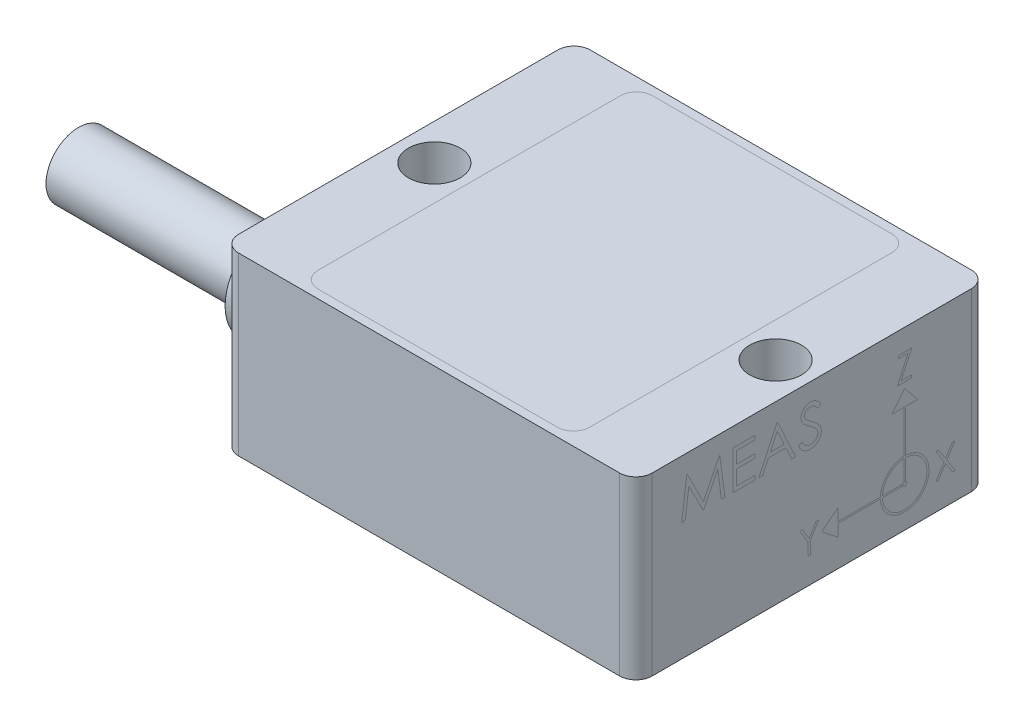
SolidWorks part; units mm, degrees
ref_plane "Front Plane" through (0, 0, 0) normal (0, 0, 1) x (1, 0, 0)
ref_plane "Top Plane" through (0, 0, 0) normal (0, 1, 0) x (1, 0, 0)
ref_plane "Right Plane" through (0, 0, 0) normal (1, 0, 0) x (0, 0, -1)
sketch "Sketch1" plane through (0, 0, 0) normal (0, 1, 0) x (1, 0, 0)
  line L0 (-10.48, 0) -> (10.48, 0) construction
  line L1 (-12.7, -10.8) -> (12.7, -10.8)
  line L2 (-12.7, -10.8) -> (-12.7, 10.8)
  line L3 (-12.7, 10.8) -> (12.7, 10.8)
  line L4 (12.7, -10.8) -> (12.7, 10.8)
  line L5 (-12.7, -10.8) -> (12.7, 10.8) construction
  line L6 (-12.7, 10.8) -> (12.7, -10.8) construction
  circle A0 centre (-10.48, 0) radius 1.59
  circle A1 centre (10.48, 0) radius 1.59
  point P0 (0, 0)
  point P10 (0, 0)
  dimension "D3" = 3.18
  dimension "D4" = 20.96
  dimension "D1" = 21.6
  dimension "D2" = 25.4
extrude "Boss-Extrude1" add sketch "Sketch1" along normal mid plane 10.8
sketch "Sketch2" plane through (0, 5.4, 0) normal (0, 1, 0) x (1, 0, 0)
  line L1 (-7.3441, -10.278) -> (7.3441, -10.278)
  line L2 (-8.3441, -9.278) -> (-8.3441, 9.278)
  line L3 (-7.3441, 10.278) -> (7.3441, 10.278)
  line L4 (8.3441, -9.278) -> (8.3441, 9.278)
  line L5 (-8.3441, -10.278) -> (8.3441, 10.278) construction
  line L6 (-8.3441, 10.278) -> (8.3441, -10.278) construction
  arc A0 (-7.3441, -10.278) -> (-8.3441, -9.278) centre (-7.3441, -9.278) cw
  arc A1 (7.3441, -10.278) -> (8.3441, -9.278) centre (7.3441, -9.278) ccw
  arc A2 (7.3441, 10.278) -> (8.3441, 9.278) centre (7.3441, 9.278) cw
  arc A3 (-8.3441, 9.278) -> (-7.3441, 10.278) centre (-7.3441, 9.278) cw
  point P0 (0, 0)
  dimension "D1" = 1
split line "Split Line1"
sketch "Sketch3" plane through (-12.7, 0, 0) normal (-1, 0, 0) x (0, 0, 1)
  circle A0 centre (5.6322, 0) radius 3
  dimension "D1" = 6
extrude "Boss-Extrude2" add sketch "Sketch3" along normal blind 2
sketch "Sketch4" plane through (-14.7, 0, 0) normal (-1, 0, 0) x (0, 0, 1)
  circle A0 centre (5.6322, 0) radius 2
  dimension "D1" = 4
extrude "Boss-Extrude3" add sketch "Sketch4" along normal blind 12
sketch "Sketch5" plane through (-26.7, 0, 0) normal (-1, 0, 0) x (0, 0, 1)
  circle A0 centre (5.6322, 0) radius 1.5
  dimension "D1" = 3
sketch "Sketch6" plane through (0, 0, -10.8) normal (0, 0, -1) x (-1, 0, 0)
  line L0 (-9.9373, -0.8014) -> (9.2984, -0.8014) construction
  text T0 "8102A-0025-036" font "Century Gothic" height in points 8
sketch "Sketch7" plane through (12.7, 0, 0) normal (1, 0, 0) x (0, 0, -1)
  line L0 (-8.1704, 1.8669) -> (0, 1.8669) construction
  line L1 (5.7097, -2.938) -> (5.7097, 1.162) construction
  line L2 (6.4989, 1.162) -> (5.7619, 1.162)
  line L3 (4.9205, 1.162) -> (5.7097, 2.1502)
  line L4 (6.4989, 1.162) -> (5.7097, 2.1502)
  line L5 (5.6575, 1.162) -> (5.6575, -1.4471)
  line L6 (5.7619, 1.162) -> (5.7619, -1.4471)
  line L7 (5.6575, 1.162) -> (4.9205, 1.162)
  line L8 (5.7097, -2.938) -> (1.6097, -2.938) construction
  line L9 (1.6097, -2.9903) -> (4.2187, -2.9903)
  line L10 (1.6097, -2.8858) -> (4.2187, -2.8858)
  line L11 (1.6097, -2.1488) -> (1.6097, -2.8858)
  line L12 (1.6097, -2.9903) -> (1.6097, -3.7272)
  line L13 (1.6097, -3.7272) -> (0.6215, -2.938)
  line L14 (1.6097, -2.1488) -> (0.6215, -2.938)
  line L15 (4.3427, -2.8858) -> (5.5947, -2.8858)
  line L16 (4.3427, -2.9903) -> (5.5947, -2.9903)
  line L17 (5.7619, -1.571) -> (5.7619, -2.823)
  line L18 (5.6575, -1.571) -> (5.6575, -2.823)
  arc A0 (4.2187, -2.9903) -> (5.7619, -1.4471) centre (5.7097, -2.938) ccw
  arc A1 (4.3427, -2.9903) -> (5.7619, -1.571) centre (5.7097, -2.938) ccw
  circle A2 centre (5.7097, -2.938) radius 0.1263
  arc A3 (5.6575, -1.4471) -> (4.2187, -2.8858) centre (5.7097, -2.938) ccw
  arc A4 (5.6575, -1.571) -> (4.3427, -2.8858) centre (5.7097, -2.938) ccw
  text T0 "MEAS" font "Century Gothic" height in points 9
  text T1 "Z" font "Century Gothic" height in points 6
  text T2 "Y" font "Century Gothic" height in points 6
  text T3 "X" font "Century Gothic" height in points 6
split line "Split Line2"
split line "Split Line3"
fillet "Fillet1" radius 1 4 edges at (12.7, 0, 10.8) (-12.7, 0, 10.8) (-12.7, 0, -10.8) (12.7, 0, -10.8)
